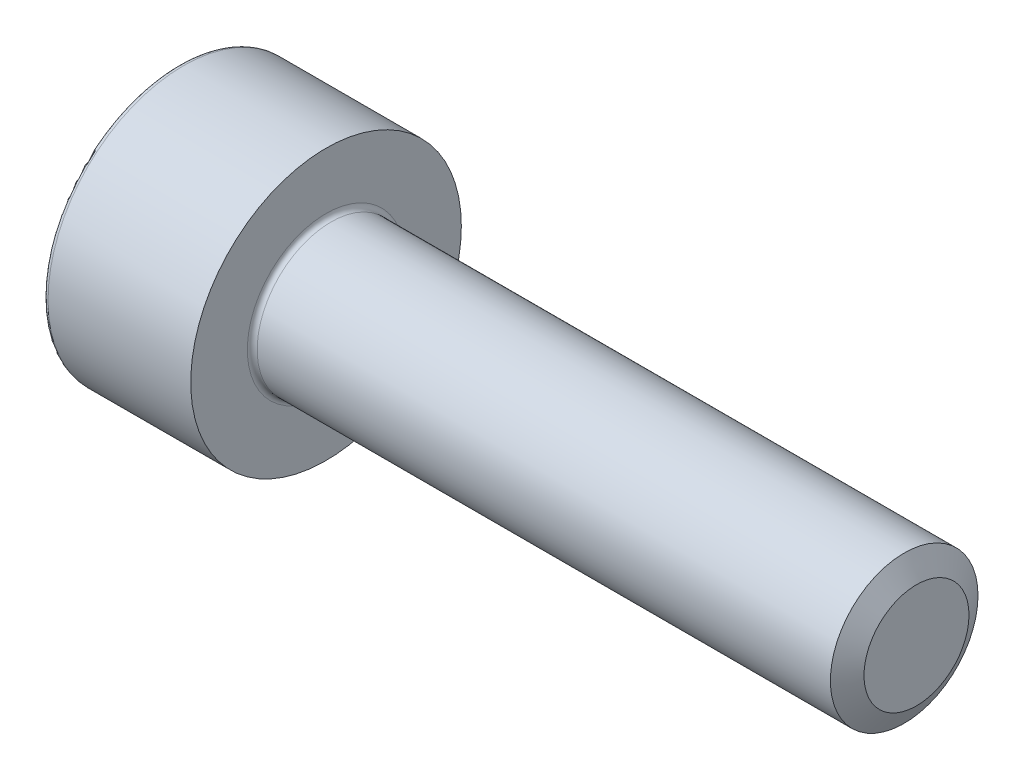
SolidWorks part; units mm, degrees
ref_plane "Front" through (0, 0, 0) normal (0, 0, 1) x (1, 0, 0)
ref_plane "Top" through (0, 0, 0) normal (0, 1, 0) x (1, 0, 0)
ref_plane "Right" through (0, 0, 0) normal (1, 0, 0) x (0, 0, -1)
sketch "草图1" plane through (0, 0, 0) normal (0, 0, 1) x (1, 0, 0)
  line L0 (0, 2.75) -> (0, 0)
  line L1 (0, 0) -> (3, 0)
  line L2 (3, 0) -> (3, 2.75)
  line L3 (3, 2.75) -> (0, 2.75)
  line L4 (0, 0) -> (3, 0) construction
revolve "旋转1" add sketch "草图1" angle 360 about L4
sketch "草图2" plane through (3, 0, 0) normal (1, 0, 0) x (0, 0, -1)
  circle A0 centre (0, 0) radius 1.5
extrude "凸台-拉伸1" add sketch "草图2" along normal blind 12
sketch "草图3" plane through (0, 0, 0) normal (-1, 0, 0) x (0, 0, 1)
  line L0 (0, 1.435) -> (-1.2427, 0.7175)
  line L1 (-1.2427, 0.7175) -> (-1.2427, -0.7175)
  line L2 (-1.2427, -0.7175) -> (0, -1.435)
  line L3 (0, -1.435) -> (1.2427, -0.7175)
  line L4 (1.2427, -0.7175) -> (1.2427, 0.7175)
  line L5 (1.2427, 0.7175) -> (0, 1.435)
extrude "切除-拉伸1" cut sketch "草图3" against normal blind 1.3
chamfer "倒角1" distance 0.433 angle 30.001 1 edges at (15, 0, -1.5)
fillet "圆角1" radius 0.1 2 edges at (3, 0, -1.5) (0, 0, -2.75)
